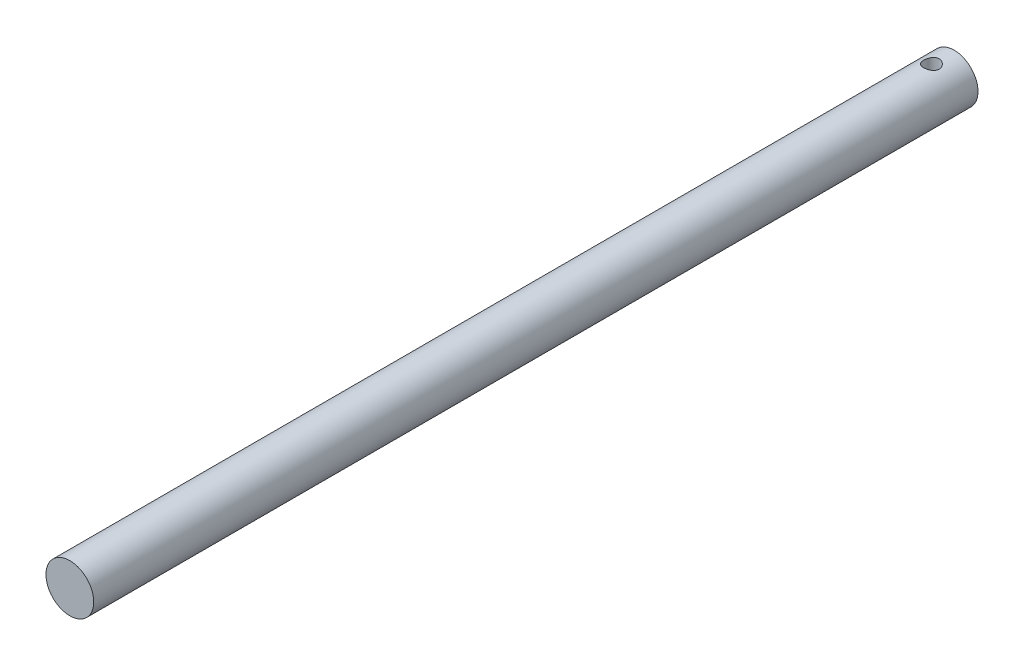
SolidWorks part; units mm, degrees
ref_plane "前视基准面" through (0, 0, 0) normal (0, 0, 1) x (1, 0, 0)
ref_plane "上视基准面" through (0, 0, 0) normal (0, 1, 0) x (1, 0, 0)
ref_plane "右视基准面" through (0, 0, 0) normal (1, 0, 0) x (0, 0, -1)
sketch "草图1" plane through (0, 0, 0) normal (0, 0, 1) x (1, 0, 0)
  circle A0 centre (0, 0) radius 10
  dimension "D1" = 20
extrude "凸台-拉伸1" add sketch "草图1" along normal blind 370
sketch "草图2" plane through (0, 0, 0) normal (0, 1, 0) x (1, 0, 0)
  line L0 (0, 19.453) -> (0, -26.2878) construction
  line L1 (10, 0) -> (-10, 0) construction
  circle A0 centre (0, -9.5) radius 3.25
  dimension "D1" = 6.5
  dimension "D2" = 9.5
extrude "切除-拉伸1" cut sketch "草图2" against normal mid plane 420
